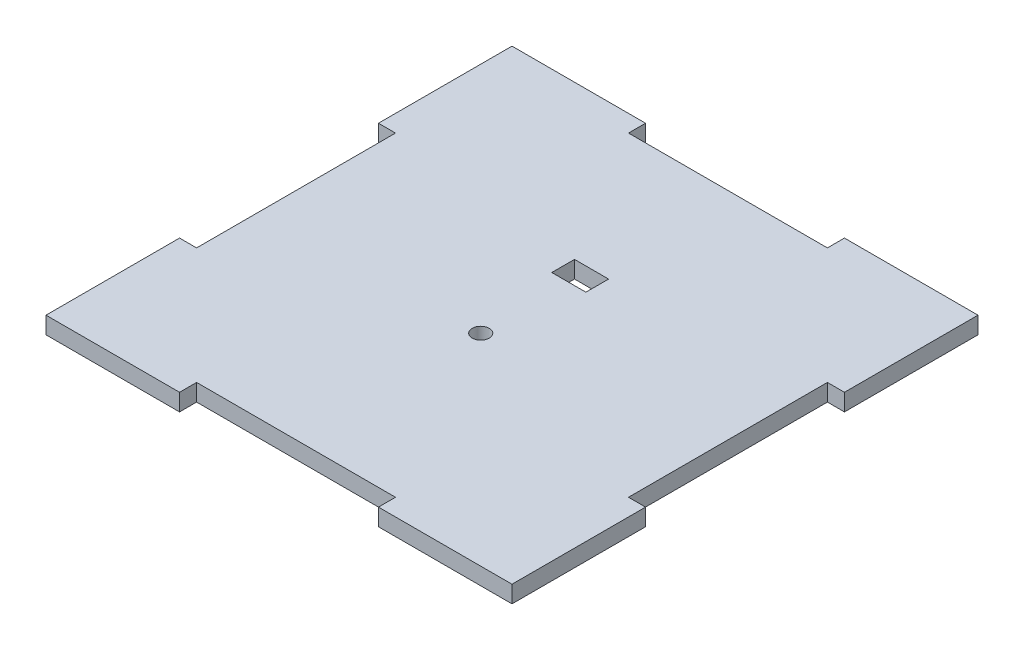
SolidWorks part; units mm, degrees
ref_plane "Front Plane" through (0, 0, 0) normal (0, 0, 1) x (1, 0, 0)
ref_plane "Top Plane" through (0, 0, 0) normal (0, 1, 0) x (1, 0, 0)
ref_plane "Right Plane" through (0, 0, 0) normal (1, 0, 0) x (0, 0, -1)
sketch "Sketch1" plane through (0, 0, 0) normal (0, 1, 0) x (1, 0, 0)
  line L0 (0, 38) -> (0, -38) construction
  line L1 (-41, -41) -> (-17.5, -41)
  line L2 (-41, -41) -> (-41, -17.5)
  line L3 (-41, 41) -> (-17.5, 41)
  line L4 (41, -41) -> (41, -17.5)
  line L5 (-41, -41) -> (41, 41) construction
  line L6 (-41, 41) -> (41, -41) construction
  line L11 (-41, 17.5) -> (-38, 17.5)
  line L12 (-38, 17.5) -> (-38, -17.5)
  line L13 (-35, 0) -> (38, 0) construction
  line L26 (17.5, 41) -> (41, 41)
  line L27 (41, 17.5) -> (41, 41)
  line L28 (17.5, -41) -> (41, -41)
  line L29 (-41, 17.5) -> (-41, 41)
  line L30 (-38, -17.5) -> (-41, -17.5)
  line L31 (-17.5, 41) -> (-17.5, 38)
  line L32 (-17.5, 38) -> (17.5, 38)
  line L33 (17.5, 38) -> (17.5, 41)
  line L34 (41, 17.5) -> (38, 17.5)
  line L35 (38, 17.5) -> (38, -17.5)
  line L36 (38, -17.5) -> (41, -17.5)
  line L37 (17.5, -41) -> (17.5, -38)
  line L38 (17.5, -38) -> (-17.5, -38)
  line L39 (-17.5, -38) -> (-17.5, -41)
  point P0 (0, 0)
  point P6 (0, 0)
  dimension "D1" = 3
  dimension "D2" = 82
  dimension "D3" = 3
  dimension "D4" = 82
  dimension "D5" = 3
  dimension "D6" = 3
extrude "Boss-Extrude1" add sketch "Sketch1" along normal blind 3
sketch "Sketch2" plane through (0, 3, 0) normal (0, 1, 0) x (1, 0, 0)
  line L1 (-3, 14) -> (3, 14)
  line L2 (-3, 14) -> (-3, 10)
  line L3 (-3, 10) -> (3, 10)
  line L4 (3, 14) -> (3, 10)
  line L5 (-3, 14) -> (3, 10) construction
  line L6 (-3, 10) -> (3, 14) construction
  circle A0 centre (0, -5.5) radius 1.5
  point P0 (0, 12)
  dimension "D3" = 3
  dimension "D1" = 6
  dimension "D2" = 4
  dimension "D4" = 5.5
  dimension "D5" = 12
  dimension "D6" = 0
extrude "Cut-Extrude1" cut sketch "Sketch2" against normal blind 3
